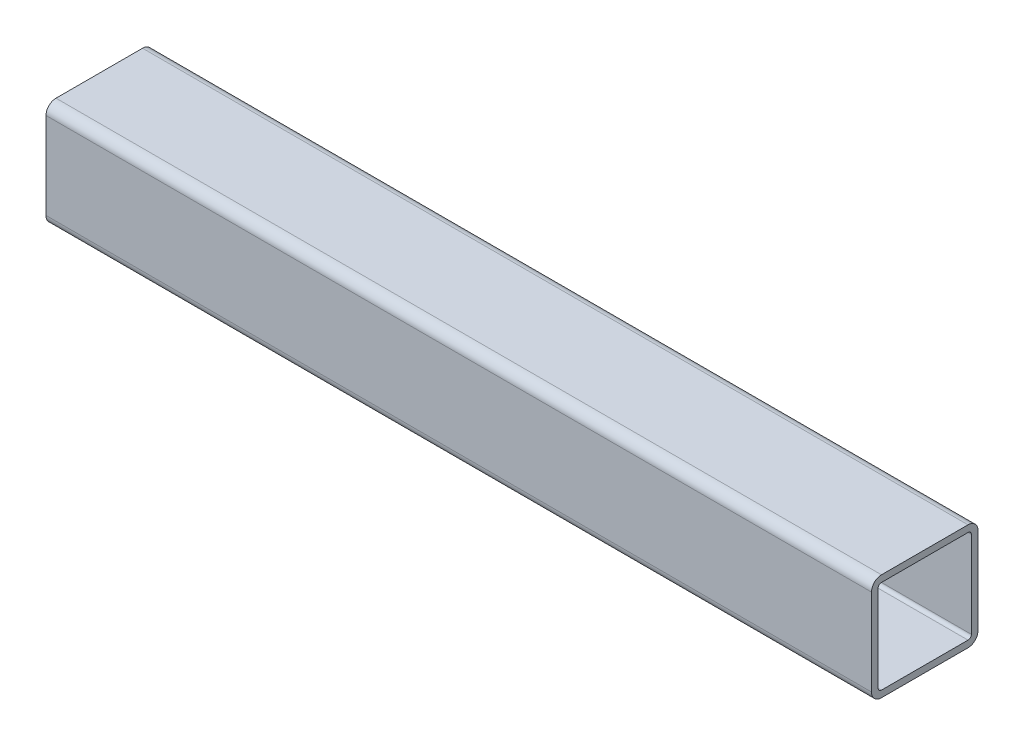
SolidWorks part; units mm, degrees
ref_plane "Front Plane" through (0, 0, 0) normal (0, 0, 1) x (1, 0, 0)
ref_plane "Top Plane" through (0, 0, 0) normal (0, 1, 0) x (1, 0, 0)
ref_plane "Right Plane" through (0, 0, 0) normal (1, 0, 0) x (0, 0, -1)
sketch "Sketch1" plane through (0, 0, 0) normal (1, 0, 0) x (0, 1, 0)
  line L1 (-20.6375, 25.4) -> (20.6375, 25.4)
  line L2 (-25.4, 20.6375) -> (-25.4, -20.6375)
  line L3 (-20.6375, -25.4) -> (20.6375, -25.4)
  line L4 (25.4, 20.6375) -> (25.4, -20.6375)
  line L5 (-25.4, 25.4) -> (25.4, -25.4) construction
  line L6 (-25.4, -25.4) -> (25.4, 25.4) construction
  line L7 (-20.6375, 22.225) -> (20.6375, 22.225)
  line L8 (-22.225, 20.6375) -> (-22.225, -20.6375)
  line L9 (-20.6375, -22.225) -> (20.6375, -22.225)
  line L10 (22.225, 20.6375) -> (22.225, -20.6375)
  line L11 (-22.225, 22.225) -> (22.225, -22.225) construction
  line L12 (-22.225, -22.225) -> (22.225, 22.225) construction
  arc A0 (-25.4, -20.6375) -> (-20.6375, -25.4) centre (-20.6375, -20.6375) ccw
  arc A1 (20.6375, -25.4) -> (25.4, -20.6375) centre (20.6375, -20.6375) ccw
  arc A2 (25.4, 20.6375) -> (20.6375, 25.4) centre (20.6375, 20.6375) ccw
  arc A3 (-20.6375, 25.4) -> (-25.4, 20.6375) centre (-20.6375, 20.6375) ccw
  arc A4 (-22.225, -20.6375) -> (-20.6375, -22.225) centre (-20.6375, -20.6375) ccw
  arc A5 (20.6375, -22.225) -> (22.225, -20.6375) centre (20.6375, -20.6375) ccw
  arc A6 (22.225, 20.6375) -> (20.6375, 22.225) centre (20.6375, 20.6375) ccw
  arc A7 (-20.6375, 22.225) -> (-22.225, 20.6375) centre (-20.6375, 20.6375) ccw
  point P0 (0, 0)
  point P6 (0, 0)
  dimension "D4" = 4.7625
  dimension "D5" = 1.5875
  dimension "D1" = 50.8
  dimension "D2" = 50.8
  dimension "D3" = 3.175
extrude "Boss-Extrude1" add sketch "Sketch1" along normal mid plane 393.7
sketch "Sketch3" plane through (-196.85, 0, 0) normal (-1, 0, 0) x (0, 0, -1)
  line L0 (0, 25.4) -> (0, -25.4) construction
  line L1 (-20.6375, 25.4) -> (20.6375, 25.4) construction
  line L2 (20.6375, -25.4) -> (-20.6375, -25.4) construction
  line L3 (-25.4, 0) -> (25.4, 0) construction
  line L4 (-25.4, -20.6375) -> (-25.4, 20.6375) construction
  line L5 (25.4, 20.6375) -> (25.4, -20.6375) construction
